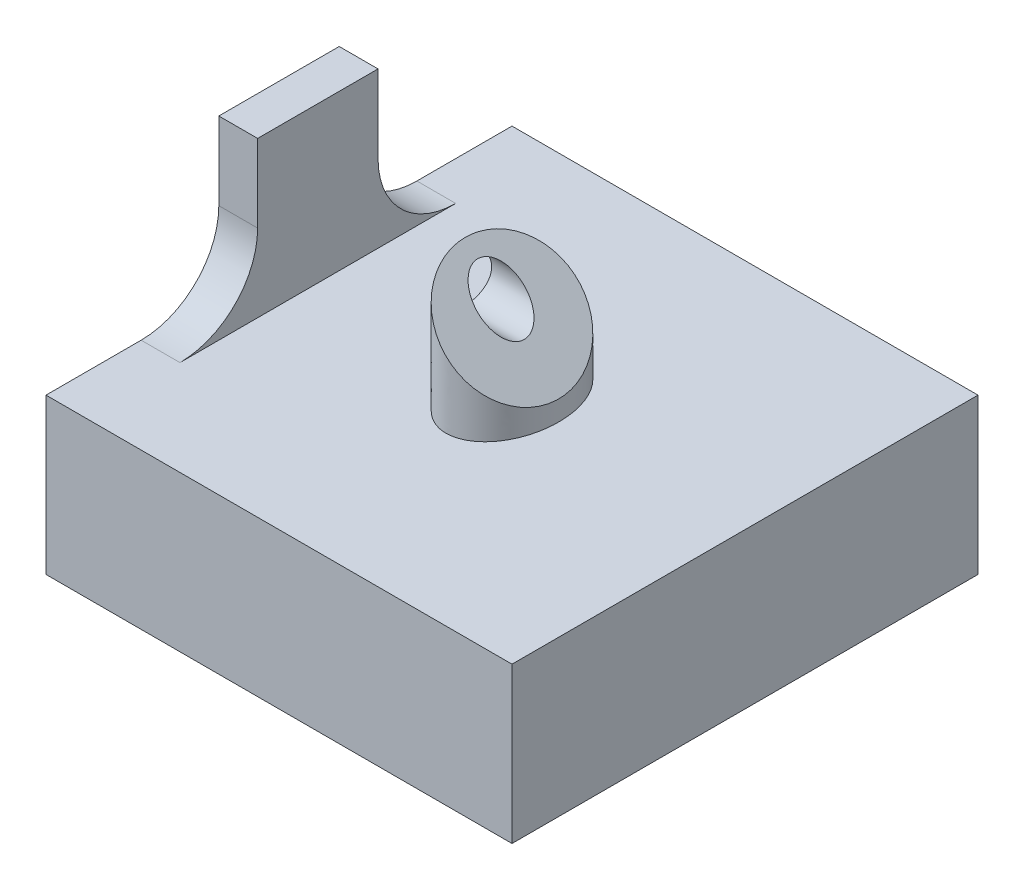
SolidWorks part; units mm, degrees
ref_plane "Front Plane" through (0, 0, 0) normal (0, 0, 1) x (1, 0, 0)
ref_plane "Top Plane" through (0, 0, 0) normal (0, 1, 0) x (1, 0, 0)
ref_plane "Right Plane" through (0, 0, 0) normal (1, 0, 0) x (0, 0, -1)
sketch "Sketch2" plane through (0, 0, 0) normal (0, 1, 0) x (1, 0, 0)
  line L0 (30, 30) -> (-30, -30) construction
  line L1 (-30, 30) -> (30, 30)
  line L2 (-30, 30) -> (-30, -30)
  line L3 (-30, -30) -> (30, -30)
  line L4 (30, 30) -> (30, -30)
  line L5 (-30, 30) -> (30, -30) construction
  point P4 (0, 0)
  dimension "D1" = 60
  dimension "D2" = 60
extrude "Boss-Extrude1" add sketch "Sketch2" along normal blind 20
sketch "Sketch3" plane through (0, 20, 0) normal (0, 1, 0) x (1, 0, 0)
  line L0 (0, -30) -> (0, 30) construction
  line L1 (-30, -30) -> (30, -30) construction
  line L2 (30, 30) -> (-30, 30) construction
sketch "Sketch4" plane through (0, 0, 30) normal (0, 0, 1) x (1, 0, 0)
  line L0 (0, 0) -> (0, 30) construction
  line L1 (0, -16.5) -> (0, 16.5) construction
  line L2 (0, 0) -> (0, 30) construction
  dimension "D1" = 30
sketch "Sketch5" plane through (0, 0, -30) normal (0, 0, -1) x (-1, 0, 0)
  line L0 (0, 0) -> (0, 30) construction
sketch3d "3DSketch2"
  line L0 (0, 30, 30) -> (0, 30, -30) construction
ref_plane "Plane1" through (15, 15, 0) normal (0.7071, 0.7071, 0) x (0, 0, -1)
sketch "Sketch7" plane through (0, 20, 0) normal (0, 1, 0) x (1, 0, 0)
  line L0 (-30, 30) -> (30, -30) construction
  line L1 (30, -30) -> (-30, -30) construction
  line L2 (-30, -30) -> (30, 30) construction
  point P8 (0, 0)
sketch3d "3DSketch3"
  line L0 (0, 20, 0) -> (0, 30, 0) construction
  dimension "D1" = 10
sketch "Sketch9" plane through (15, 15, 0) normal (0.7071, 0.7071, 0) x (0, 0, -1)
  line L0 (-30, 21.2132) -> (30, 21.2132) construction
  circle A0 centre (0, 21.2132) radius 8.5
sketch "Sketch10" plane through (0, 20, 0) normal (0, 1, 0) x (1, 0, 0)
  line L0 (0, -30) -> (0, 30) construction
  ellipse E0 centre (0, 0) end of major axis (0, 8.5) minor radius 6.0104
  ellipse E1 centre (0, 0) end of major axis (0, -8.5) minor radius 6.0104 construction
sketch3d "3DSketch4"
  line L0 (-6.0104, 20, 0) -> (-6.0104, 36.0104, 0) construction
  circle A0 centre (0, 30, 0) radius 8.5 construction
  point P5 (6.0104, 36.0104, 0)
loft "Loft1" add profiles "Sketch9", "Sketch10"
sketch "Sketch12" plane through (30, 0, 0) normal (1, 0, 0) x (0, 0, -1)
  line L0 (-30, 30) -> (30, 30) construction
  circle A0 centre (0, 30) radius 3
extrude "Cut-Extrude1" cut sketch "Sketch12" against normal through all
sketch "Sketch13" plane through (0, 20, 0) normal (0, 1, 0) x (1, 0, 0)
  circle A0 centre (0, 0) radius 3
extrude "Cut-Extrude2" cut sketch "Sketch13" against normal through all
sketch "Sketch15" plane through (0, 20, 0) normal (0, 1, 0) x (1, 0, 0)
  line L0 (-30, 0) -> (30, 0) construction
  line L1 (-30, 30) -> (-30, -30) construction
  line L2 (30, -30) -> (30, 30) construction
  line L4 (-30, -7.75) -> (-25, -7.75)
  line L5 (-30, -7.75) -> (-30, 7.75)
  line L6 (-30, 7.75) -> (-25, 7.75)
  line L7 (-25, -7.75) -> (-25, 7.75)
  dimension "D1" = 15.5
  dimension "D2" = 5
extrude "Boss-Extrude2" add sketch "Sketch15" along normal blind 20
sketch "Sketch16" plane through (-30, 0, 0) normal (-1, 0, 0) x (0, 0, 1)
  circle A0 centre (0, 30) radius 3
fillet "Fillet1" radius 10 2 edges at (-27.5, 20, -7.75) (-27.5, 20, 7.75)
sketch3d "3DSketch5"
  line L0 (6.0104, 23.9896, 0) -> (6.0104, 23.9896, 20.993)
  circle A0 centre (0, 30, 0) radius 8.5 construction
  point P0 (6.0104, 23.9896, 0)
  point P4 (6.0104, 36.0104, 0)
ref_plane "Plane2" through (-8.9896, 8.9896, 0) normal (-0.7071, 0.7071, 0) x (0, 0, 1)
sketch "Sketch17" plane through (-8.9896, 8.9896, 0) normal (-0.7071, 0.7071, 0) x (0, 0, 1)
  line L0 (30, 21.2132) -> (-30, 21.2132) construction
  line L1 (-13.8829, 21.2132) -> (14.2291, 21.2132)
  line L2 (-13.8829, 21.2132) -> (-13.8829, 20.2132)
  line L3 (-13.8829, 20.2132) -> (14.2291, 20.2132)
  line L4 (14.2291, 21.2132) -> (14.2291, 20.2132)
  dimension "D1" = 1
extrude "Cut-Extrude3" cut sketch "Sketch17" along normal blind 23 and the other way blind 3
